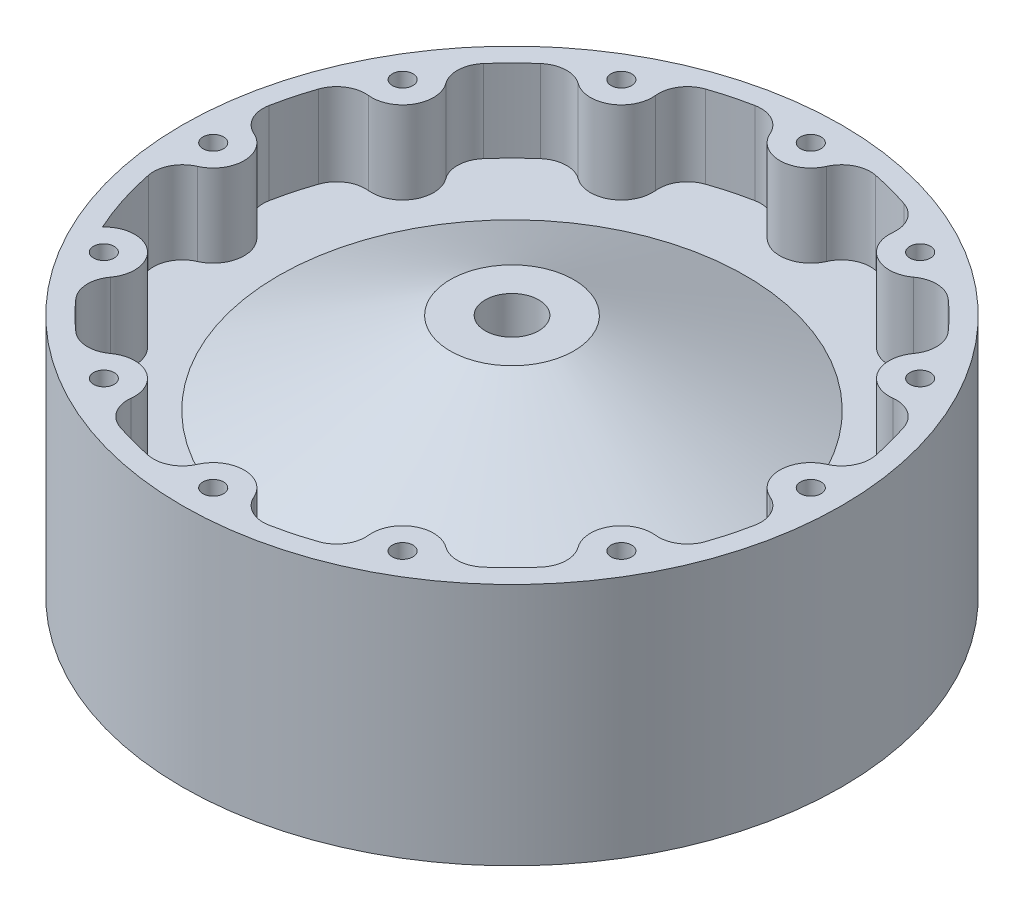
SolidWorks part; units mm, degrees
material "6061-T6 (SS)"
ref_plane "Front Plane" through (0, 0, 0) normal (0, 0, 1) x (1, 0, 0)
ref_plane "Top Plane" through (0, 0, 0) normal (0, 1, 0) x (1, 0, 0)
ref_plane "Right Plane" through (0, 0, 0) normal (1, 0, 0) x (0, 0, -1)
ref_plane "Plane1" through (0, 0, -75.0887) normal (0, 0, 1) x (1, 0, 0)
sketch "Sketch1" plane through (0, 0, 0) normal (0, 1, 0) x (1, 0, 0)
  line L1 (95.25, 0) -> (101.6, 0)
  line L2 (0, 0) -> (0, 61.9125) construction
  line L4 (101.6, 61.1187) -> (101.6, 0)
  line L6 (101.6, 61.1187) -> (8.255, 61.1187) construction
  line L8 (0, 75.0887) -> (101.6, 75.0887)
  line L9 (101.6, 75.0887) -> (101.6, 61.1187)
  line L10 (8.255, 0) -> (8.255, 75.0887)
  line L11 (8.255, 75.0887) -> (-8.255, 75.0887)
  line L12 (-8.255, 75.0887) -> (-8.255, 0)
  line L13 (-8.255, 0) -> (8.255, 0)
  line L14 (8.255, 61.1187) -> (0, 61.1187) construction
  line L15 (19.05, 75.0887) -> (71.9667, 49.6887)
  line L17 (95.25, 49.6887) -> (95.25, 75.0887)
  line L18 (95.25, 49.6887) -> (71.9667, 49.6887)
  ellipse E0 centre (0, 0) end of major axis (-95.25, 0) minor radius 61.1187
  point P18 (19.05, 75.0887)
  dimension "D4" = 13.97
  dimension "D6" = 16.51
  dimension "D7" = 6.35
  dimension "D10" = 19.05
  dimension "D2" = 101.6
  dimension "D3" = 75.0887
  dimension "D5" = 25.4
revolve "Revolve1" add sketch "Sketch1" angle 360 about L2
sketch "Sketch13" plane through (0, 0, 0) normal (0, 0, 1) x (1, 0, 0)
  line L0 (-67.9108, -66.7883) -> (66.7883, 67.9108)
  line L1 (-66.7883, -67.9108) -> (67.9108, 66.7883)
  line L2 (0, 0) -> (0, -28.3739) construction
  circle A4 centre (0, 0) radius 95.25 construction
  arc A5 (-67.9108, -66.7883) -> (-66.7883, -67.9108) centre (0, 0) ccw
  arc A6 (66.7883, 67.9108) -> (67.9108, 66.7883) centre (0, 0) cw
  dimension "D1" = 1.5875
  dimension "D2" = 135
sketch "Sketch14" plane through (0, 0, -75.0888) normal (0, 0, -1) x (-1, 0, 0)
  circle A0 centre (0, 0) radius 8.255
  circle A1 centre (0, 0) radius 8.255 construction
sketch "Sketch15" plane through (0, 0, -75.0888) normal (0, 0, -1) x (-1, 0, 0)
  circle A0 centre (0, 0) radius 95.25
  circle A3 centre (0, -92.075) radius 9.525
  circle A4 centre (0, 0) radius 101.6 construction
  circle A5 centre (0, 0) radius 95.25 construction
  circle M2 centre (0, 0) radius 95.25
  dimension "D1" = 19.05
extrude "Boss-Extrude3" add sketch "Sketch15" against normal up to body contours A3 M2
sketch "Sketch16" plane through (0, 0, -75.0888) normal (0, 0, -1) x (-1, 0, 0)
  line L0 (0, 0) -> (0, -92.075) construction
  circle A0 centre (0, -92.075) radius 3.175
  circle A2 centre (0, 0) radius 95.25 construction
  arc A3 (9.1233, -94.8121) -> (-9.1233, -94.8121) centre (0, 0) ccw construction
  dimension "D1" = 6.35
sketch "Sketch17" plane through (0, 0, -75.0888) normal (0, 0, -1) x (-1, 0, 0)
  line L0 (0, 0) -> (0, -101.6) construction
  line L2 (0, -95.25) -> (16.9112, -95.25) construction
  line L3 (0, -82.55) -> (13.8103, -82.55) construction
  line L4 (0, -88.9) -> (10.3365, -88.9) construction
  circle A0 centre (0, -92.075) radius 3.175
  circle A1 centre (0, 0) radius 101.6 construction
  arc A3 (9.1233, -94.8121) -> (-9.1233, -94.8121) centre (0, -92.075) ccw construction
  dimension "D1" = 6.35
  dimension "D2" = 6.35
extrude "Cut-Extrude5" cut sketch "Sketch17" against normal blind 25.4
pattern_circular "CirPattern5" count 12 over 360 about axis through (0, 0, 0) along (0, 0, 1) of "Boss-Extrude3", "Cut-Extrude5"
fillet "Fillet2" radius 8.89 23 edges at (-9.1233, 94.8121, -62.3887) (9.1233, 94.8121, -62.3887) (39.505, 86.6713, -62.3887) (55.307, 77.548, -62.3887) (77.548, 55.307, -62.3887) (86.6713, 39.505, -62.3887) (94.8121, 9.1233, -62.3887) (94.8121, -9.1233, -62.3887) (86.6713, -39.505, -62.3887) (77.548, -55.307, -62.3887) (55.307, -77.548, -62.3887) (39.505, -86.6713, -62.3887) (9.1233, -94.8121, -62.3887) (-9.1233, -94.8121, -62.3887) (-39.505, -86.6713, -62.3887) (-55.307, -77.548, -62.3887) (-77.548, -55.307, -62.3887) (-86.6713, -39.505, -62.3887) (-94.8121, -9.1233, -62.3887) (-94.8121, 9.1233, -62.3887) (-77.548, 55.307, -62.3887) (-55.307, 77.548, -62.3887) (-39.505, 86.6713, -62.3887)
move or copy body "Body-Move/Copy1" bodies to move or copy 124 copy no rotation origin (0, 0, -37.5444) rotation axis (1, 0, 0) rotation angle 90
equation "\"D7@Sketch1\"= .25"
equation "\"D1@Plane1\"= \"D3@Sketch1\""
